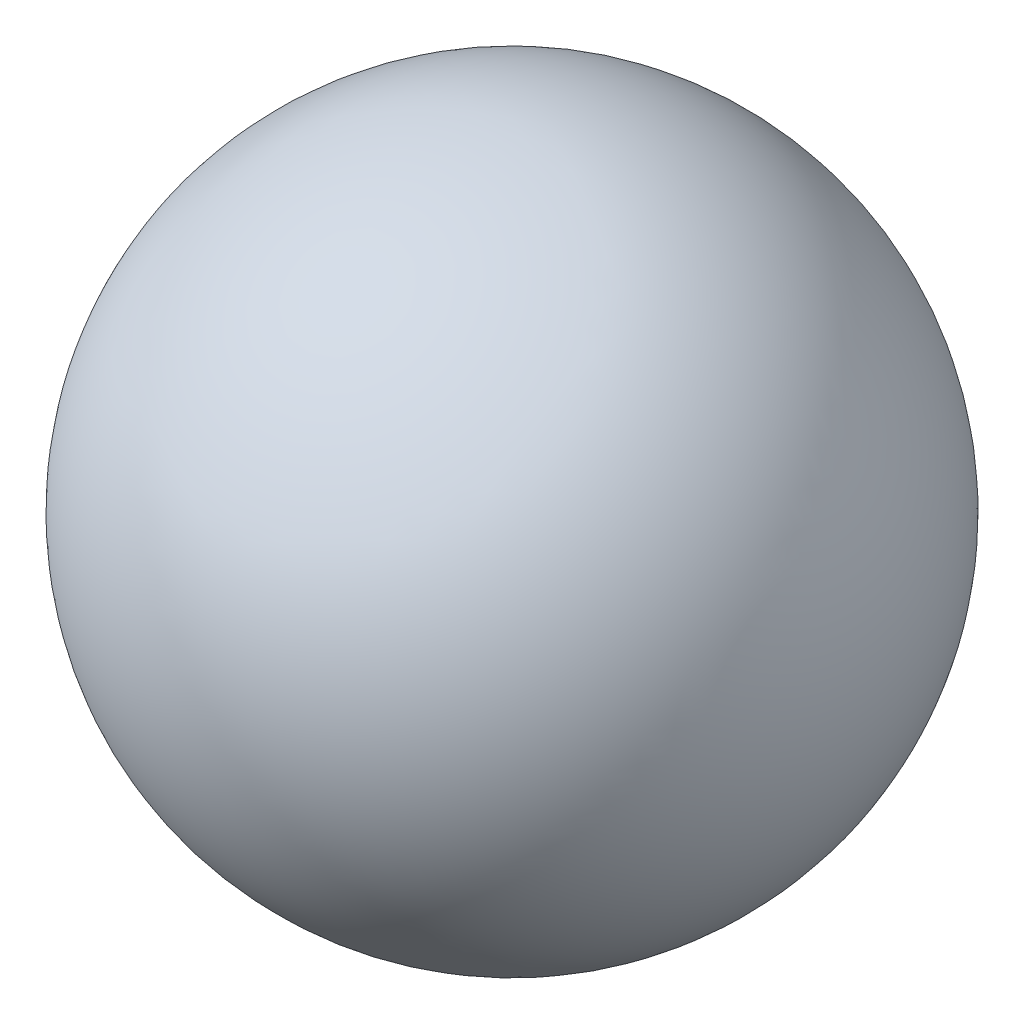
SolidWorks part; units mm, degrees
ref_plane "Front Plane" through (0, 0, 0) normal (0, 0, 1) x (1, 0, 0)
ref_plane "Top Plane" through (0, 0, 0) normal (0, 1, 0) x (1, 0, 0)
ref_plane "Right Plane" through (0, 0, 0) normal (1, 0, 0) x (0, 0, -1)
sketch "Sketch1" plane through (0, 0, 0) normal (0, 1, 0) x (1, 0, 0)
  line L0 (-50, 0) -> (50, 0)
  arc A0 (50, 0) -> (-50, 0) centre (0, 0) ccw
revolve "Revolve1" add sketch "Sketch1" angle 360 about L0
